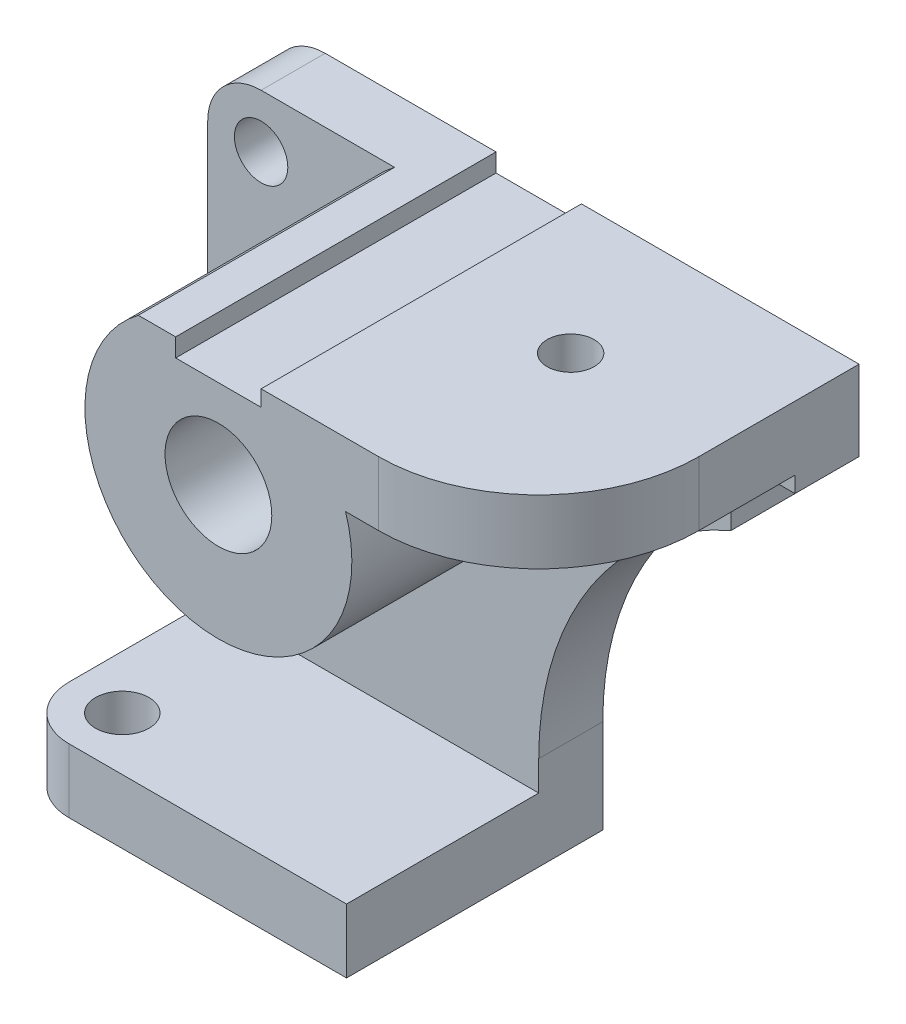
SolidWorks part; units mm, degrees
ref_plane "Front Plane" through (0, 0, 0) normal (0, 0, 1) x (1, 0, 0)
ref_plane "Top Plane" through (0, 0, 0) normal (0, 1, 0) x (1, 0, 0)
ref_plane "Right Plane" through (0, 0, 0) normal (1, 0, 0) x (0, 0, -1)
sketch "Sketch2" plane through (0, 0, 0) normal (0, 0, 1) x (1, 0, 0)
  line L0 (0, 0) -> (-50, 0)
  line L1 (-50, 0) -> (-50, 90)
  line L2 (-40, 100) -> (-8, 100)
  line L3 (-8, 100) -> (-8, 96.5724)
  line L4 (-8, 96.5724) -> (8, 96.5724)
  line L5 (8, 96.5724) -> (8, 99.5724)
  line L6 (8, 99.5724) -> (60, 99.5724)
  line L7 (60, 99.5724) -> (60, 84.5724)
  line L8 (60, 84.5724) -> (48, 84.5724)
  line L12 (48, 84.5724) -> (48, 72.5724)
  line L13 (0, 0) -> (0, 96.5724) construction
  line L15 (12, 0) -> (0, 0)
  line L16 (12, 0) -> (12, 17.5815)
  arc A2 (12, 17.5815) -> (48, 72.5724) centre (72, 17.5815) cw
  arc A3 (-40, 100) -> (-50, 90) centre (-40, 90) ccw
  circle A4 centre (-40, 90) radius 5
  circle A5 centre (0, 80) radius 10
  point P17 (-50, 100)
  point P21 (0, 0)
  dimension "D10" = 12
  dimension "D2" = 60
  dimension "D11" = 10
  dimension "D12" = 10
  dimension "D13" = 20
  dimension "D1" = 50
  dimension "D3" = 100
  dimension "D4" = 15
  dimension "D5" = 12
  dimension "D6" = 12
  dimension "D7" = 16
  dimension "D8" = 3
  dimension "D9" = 110
  dimension "D14" = 80
extrude "Boss-Extrude2" add sketch "Sketch2" along normal blind 12
sketch "Sketch3" plane through (0, 0, 0) normal (0, -1, 0) x (1, 0, 0)
  line L0 (-50, 0) -> (-50, 38)
  line L1 (-40, 48) -> (12, 48)
  line L2 (12, 48) -> (12, 0)
  line L3 (12, 0) -> (-50, 0)
  arc A0 (-40, 48) -> (-50, 38) centre (-40, 38) ccw
  circle A1 centre (-40, 38) radius 5
  point P8 (-50, 48)
  dimension "D3" = 10
  dimension "D4" = 10
  dimension "D1" = 62
  dimension "D2" = 48
extrude "Boss-Extrude3" add sketch "Sketch3" against normal blind 12
sketch "Sketch4" plane through (0, 0, 12) normal (0, 0, 1) x (1, 0, 0)
  line L0 (60, 99.5724) -> (8, 99.5724) construction
  line L1 (8, 99.5724) -> (8, 96.5724) construction
  line L2 (8, 96.5724) -> (-8, 96.5724) construction
  line L3 (-8, 96.5724) -> (-8, 100) construction
  line L4 (-8, 100) -> (-40, 100) construction
  line L5 (60, 99.5724) -> (8, 99.5724)
  line L6 (8, 99.5724) -> (8, 96.5724)
  line L7 (8, 96.5724) -> (-8, 96.5724)
  line L8 (-8, 96.5724) -> (-8, 100)
  line L9 (-8, 100) -> (-40, 100)
  arc A0 (-15, 100) -> (15.5538, 99.5724) centre (0, 80) ccw
  circle A1 centre (0, 80) radius 10 construction
  circle A2 centre (0, 80) radius 10
  dimension "D1" = 50
extrude "Boss-Extrude4" add sketch "Sketch4" along normal blind 48
sketch "Sketch5" plane through (0, 99.5724, 0) normal (0, 1, 0) x (1, 0, 0)
  line L0 (8, -60) -> (8, 0)
  line L1 (8, 0) -> (60, 0)
  line L2 (60, 0) -> (60, -12)
  line L3 (60, -12) -> (60, -30)
  line L4 (-25, -60) -> (25, -60) construction
  line L5 (30, -60) -> (8, -60)
  arc A0 (60, -30) -> (30, -60) centre (30, -30) cw
  dimension "D1" = 30
extrude "Boss-Extrude5" add sketch "Sketch5" against normal blind 12
sketch "Sketch6" plane through (0, 99.5724, 0) normal (0, 1, 0) x (1, 0, 0)
  circle A0 centre (31.2021, -25.2246) radius 4.4
  dimension "D1" = 8.8
extrude "Cut-Extrude1" cut sketch "Sketch6" against normal through all
